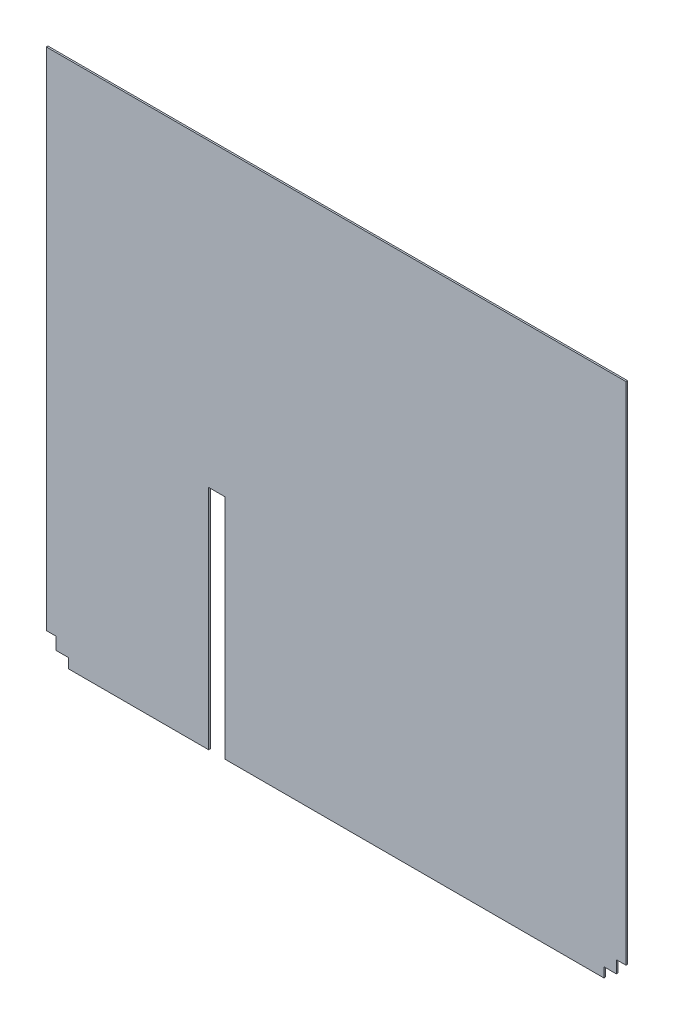
SolidWorks part; units mm, degrees
ref_plane "Front Plane" through (0, 0, 0) normal (0, 0, 1) x (1, 0, 0)
ref_plane "Top Plane" through (0, 0, 0) normal (0, 1, 0) x (1, 0, 0)
ref_plane "Right Plane" through (0, 0, 0) normal (1, 0, 0) x (0, 0, -1)
sketch "Sketch1" plane through (0, 0, 0) normal (0, 0, 1) x (1, 0, 0)
  line L0 (0, 34.544) -> (15.24, 34.544)
  line L1 (0, 0) -> (907.001, 0)
  line L2 (0, 0) -> (0, 825.5)
  line L3 (0, 825.5) -> (907.001, 825.5)
  line L4 (907.001, 0) -> (907.001, 825.5)
  line L5 (0, 0) -> (914.4, 0) construction
  line L6 (0, 0) -> (0, 914.4) construction
  line L7 (0, 914.4) -> (914.4, 914.4) construction
  line L8 (914.4, 0) -> (914.4, 914.4) construction
  line L9 (15.24, 34.544) -> (15.24, 15.24)
  line L10 (15.24, 15.24) -> (34.544, 15.24)
  line L11 (34.544, 15.24) -> (34.544, 0)
  line L12 (907.001, 34.544) -> (891.761, 34.544)
  line L13 (891.761, 34.544) -> (891.761, 15.24)
  line L14 (891.761, 15.24) -> (872.457, 15.24)
  line L15 (872.457, 15.24) -> (872.457, 0)
  line L16 (254, 0) -> (254, 355.6)
  line L17 (254, 355.6) -> (279.4, 355.6)
  line L18 (279.4, 355.6) -> (279.4, 0)
  dimension "D1" = 825.5
  dimension "D2" = 907.001
  dimension "D3" = 914.4
  dimension "D4" = 914.4
  dimension "D5" = 15.24
  dimension "D6" = 15.24
  dimension "D7" = 34.544
  dimension "D8" = 34.544
  dimension "D9" = 15.24
  dimension "D10" = 15.24
  dimension "D11" = 34.544
  dimension "D12" = 34.544
  dimension "D14" = 355.6
  dimension "D15" = 25.4
  dimension "D17" = 254
extrude "Boss-Extrude1" add sketch "Sketch1" along normal blind 2.54 contours L15 L14 L13 L12 L4 L3 L2 L0 L9 L10 L11 L1
